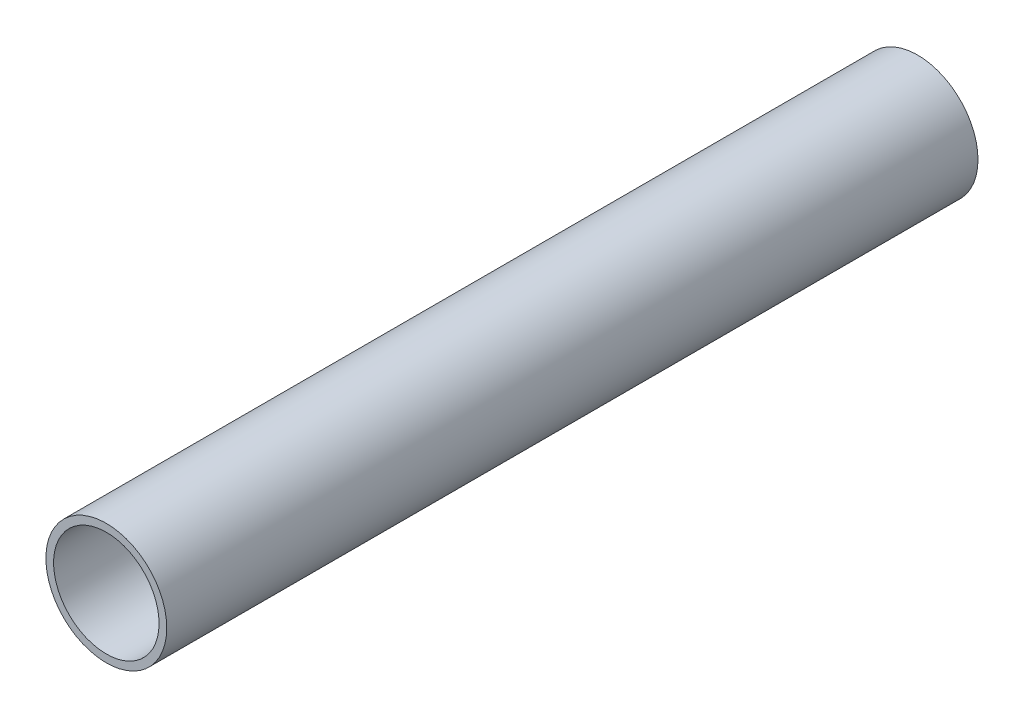
SolidWorks part; units mm, degrees
material "PVC Rigid"
ref_plane "Front Plane" through (0, 0, 0) normal (0, 0, 1) x (1, 0, 0)
ref_plane "Top Plane" through (0, 0, 0) normal (0, 1, 0) x (1, 0, 0)
ref_plane "Right Plane" through (0, 0, 0) normal (1, 0, 0) x (0, 0, -1)
sketch "Sketch1" plane through (0, 0, 0) normal (0, 0, 1) x (1, 0, 0)
  circle A0 centre (0, 0) radius 18.923
  circle A1 centre (0, 0) radius 16.51
  dimension "D1" = 37.846
  dimension "D2" = 33.02
extrude "Boss-Extrude1" add sketch "Sketch1" along normal blind 254
